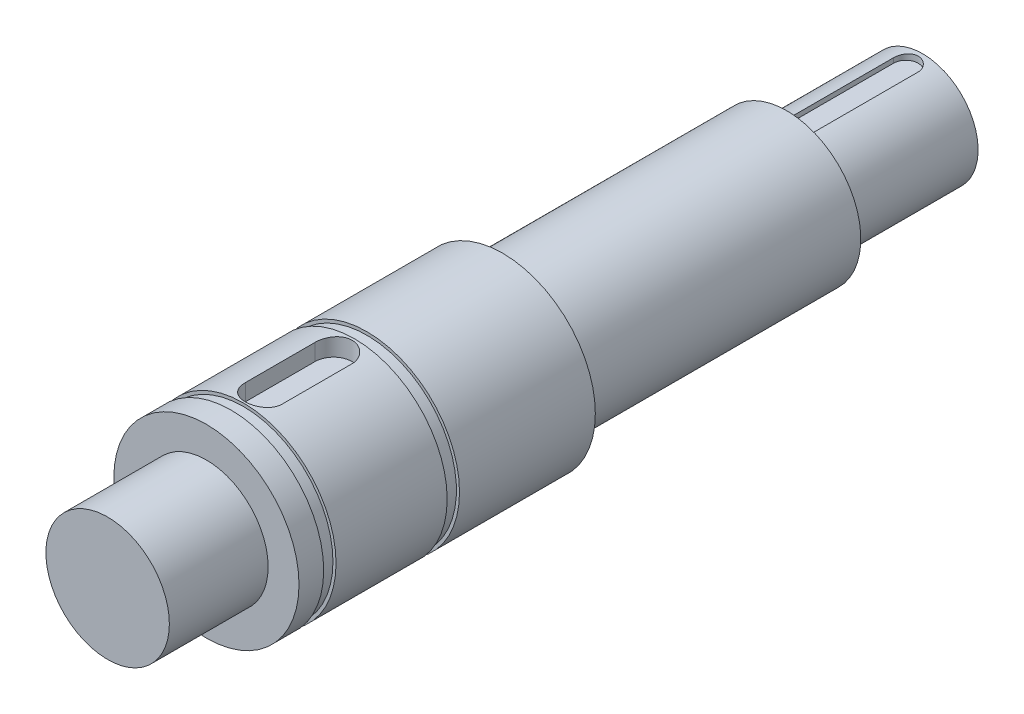
SolidWorks part; units mm, degrees
ref_plane "Plan de face" through (0, 0, 0) normal (0, 0, 1) x (1, 0, 0)
ref_plane "Plan de dessus" through (0, 0, 0) normal (0, 1, 0) x (1, 0, 0)
ref_plane "Plan de droite" through (0, 0, 0) normal (1, 0, 0) x (0, 0, -1)
sketch "Esquisse1" plane through (0, 0, 0) normal (0, 0, 1) x (1, 0, 0)
  circle A0 centre (0, 0) radius 5
  dimension "D1" = 10
extrude "Boss.-Extru.1" add sketch "Esquisse1" along normal blind 8
sketch "Esquisse2" plane through (0, 0, 0) normal (0, 0, 1) x (1, 0, 0)
  circle A0 centre (0, 0) radius 7.5
  dimension "D1" = 15
extrude "Boss.-Extru.3" add sketch "Esquisse2" against normal blind 2
sketch "Esquisse5" plane through (0, 0, -2) normal (0, 0, -1) x (-1, 0, 0)
  circle A0 centre (0, 0) radius 7.25
  dimension "D1" = 14.5
extrude "Boss.-Extru.6" add sketch "Esquisse5" along normal blind 1
sketch "Esquisse8" plane through (0, 0, -3) normal (0, 0, -1) x (-1, 0, 0)
  circle A0 centre (0, 0) radius 7.5
  dimension "D1" = 15
extrude "Boss.-Extru.8" add sketch "Esquisse8" along normal blind 9
sketch "Esquisse9" plane through (0, 0, -12) normal (0, 0, -1) x (-1, 0, 0)
  circle A0 centre (0, 0) radius 7.25
  dimension "D1" = 14.5
extrude "Boss.-Extru.9" add sketch "Esquisse9" along normal blind 1
sketch "Esquisse10" plane through (0, 0, -13) normal (0, 0, -1) x (-1, 0, 0)
  circle A0 centre (0, 0) radius 7.5
  dimension "D1" = 15
extrude "Boss.-Extru.10" add sketch "Esquisse10" along normal blind 11
sketch "Esquisse11" plane through (0, 0, -24) normal (0, 0, -1) x (-1, 0, 0)
  circle A0 centre (0, 0) radius 6
  dimension "D1" = 12
extrude "Boss.-Extru.11" add sketch "Esquisse11" along normal blind 23
sketch "Esquisse12" plane through (0, 0, -47) normal (0, 0, -1) x (-1, 0, 0)
  circle A0 centre (0, 0) radius 4.5
  dimension "D1" = 9
extrude "Boss.-Extru.12" add sketch "Esquisse12" along normal blind 11
sketch "Esquisse14" plane through (0, 0, 0) normal (0, 1, 0) x (1, 0, 0)
  line L0 (0, 4.65) -> (0, 10.3) construction
  line L1 (-1.5, 4.65) -> (-1.5, 10.3)
  line L2 (1.5, 4.65) -> (1.5, 10.3)
  line L3 (7.5, 12) -> (-7.5, 12) construction
  arc A0 (-1.5, 4.65) -> (1.5, 4.65) centre (0, 4.65) ccw
  arc A1 (1.5, 10.3) -> (-1.5, 10.3) centre (0, 10.3) ccw
  point P3 (0, 7.475)
  dimension "D1" = 5.65
  dimension "D2" = 3
  dimension "D3" = 1.7
extrude "Enlèv. mat.-Extru.7" cut sketch "Esquisse14" along normal blind 5 from offset 6
sketch "Esquisse15" plane through (0, 0, 0) normal (0, 1, 0) x (1, 0, 0)
  line L0 (0, 48.15) -> (0, 56.65) construction
  line L1 (-1, 48.15) -> (-1, 56.65)
  line L2 (1, 48.15) -> (1, 56.65)
  line L3 (4.5, 58) -> (-4.5, 58) construction
  arc A0 (-1, 48.15) -> (1, 48.15) centre (0, 48.15) ccw
  arc A1 (1, 56.65) -> (-1, 56.65) centre (0, 56.65) ccw
  point P3 (0, 52.4)
  dimension "D3" = 1.35
  dimension "D1" = 2
  dimension "D2" = 8.5
extrude "Enlèv. mat.-Extru.9" cut sketch "Esquisse15" along normal blind 5 from offset 4
sketch "Esquisse17" plane through (0, 0, -58) normal (0, 0, -1) x (-1, 0, 0)
  circle A0 centre (0, 0) radius 2.25
  dimension "D1" = 4.5
extrude "Enlèv. mat.-Extru.10" cut sketch "Esquisse17" against normal blind 5
